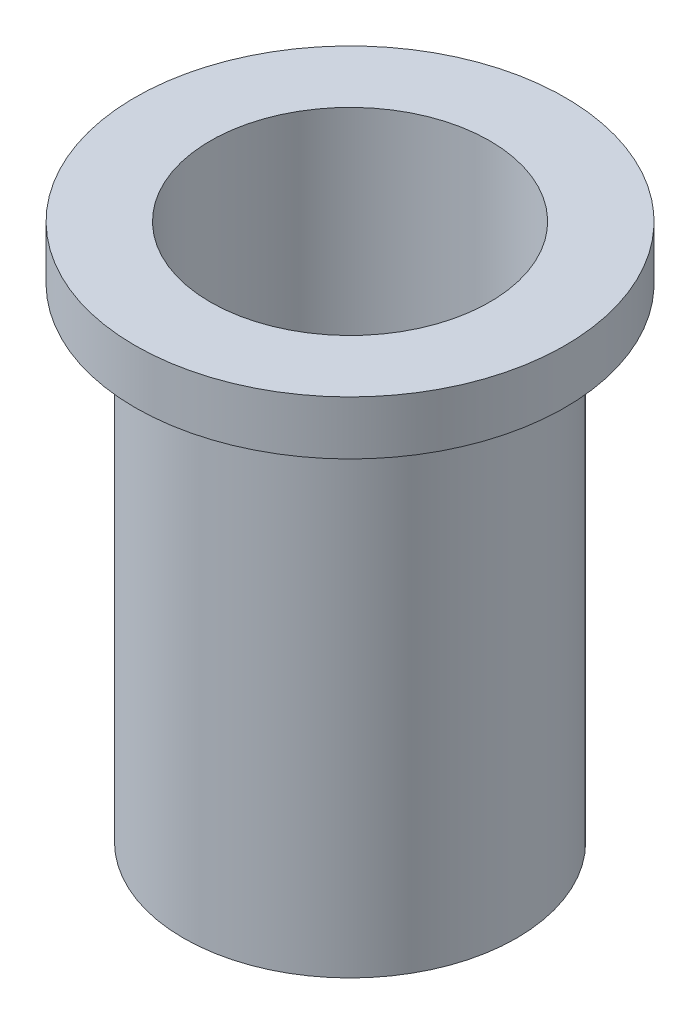
SolidWorks part; units mm, degrees
ref_plane "Front Plane" through (0, 0, 0) normal (0, 0, 1) x (1, 0, 0)
ref_plane "Top Plane" through (0, 0, 0) normal (0, 1, 0) x (1, 0, 0)
ref_plane "Right Plane" through (0, 0, 0) normal (1, 0, 0) x (0, 0, -1)
sketch "Sketch1" plane through (0, 0, 0) normal (0, 1, 0) x (1, 0, 0)
  circle A0 centre (0, 0) radius 7.874
  circle A1 centre (0, 0) radius 6.604
  dimension "D1" = 15.748
  dimension "D2" = 13.208
extrude "Boss-Extrude1" add sketch "Sketch1" along normal blind 25.4
sketch "Sketch2" plane through (0, 25.4, 0) normal (0, 1, 0) x (1, 0, 0)
  circle A0 centre (0, 0) radius 10.16
  dimension "D1" = 20.32
extrude "Extrude-Thin1" add sketch "Sketch2" against normal blind 2.54 thin thin type one direction reverse wall 2.54
